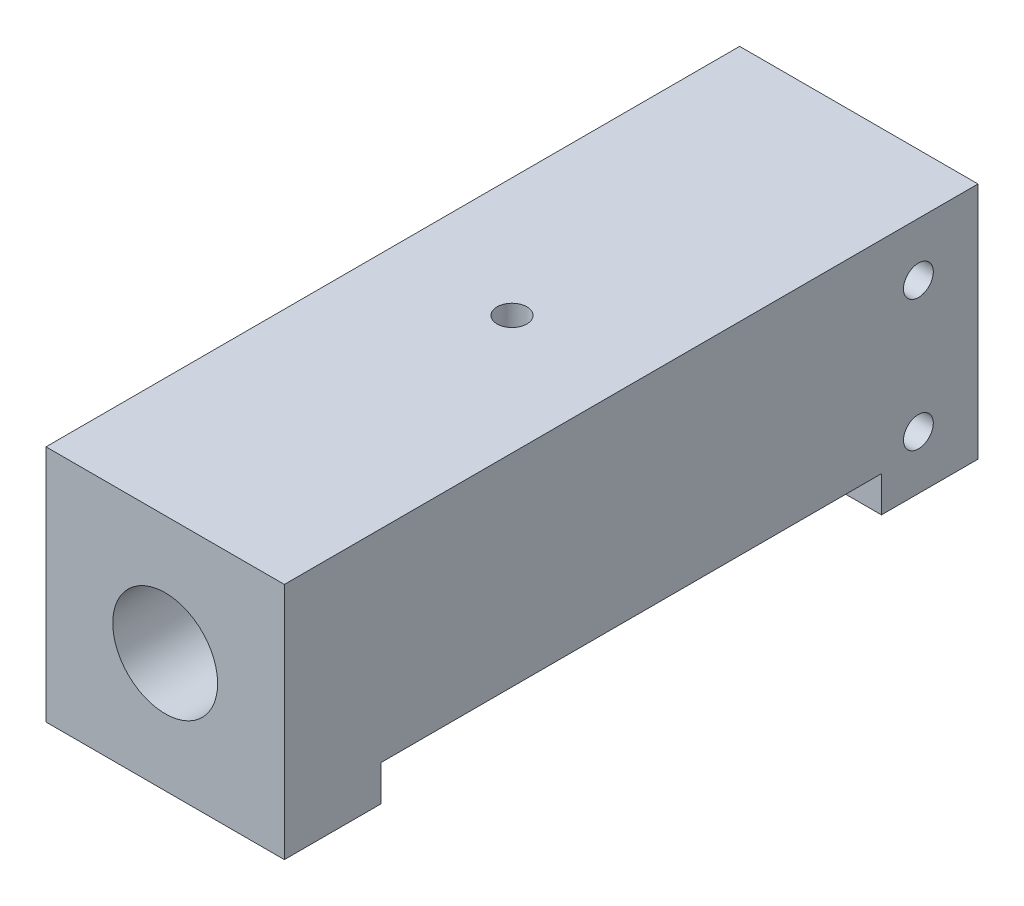
SolidWorks part; units mm, degrees
material "6063-T5"
ref_plane "Piano frontale" through (0, 0, 0) normal (0, 0, 1) x (1, 0, 0)
ref_plane "Piano superiore" through (0, 0, 0) normal (0, 1, 0) x (1, 0, 0)
ref_plane "Piano destro" through (0, 0, 0) normal (1, 0, 0) x (0, 0, -1)
sketch "Schizzo1" plane through (0, 0, 0) normal (0, 0, 1) x (1, 0, 0)
  line L1 (10, -10) -> (-10, -10)
  line L2 (10, -10) -> (10, 10)
  line L3 (10, 10) -> (-10, 10)
  line L4 (-10, -10) -> (-10, 10)
  line L5 (10, -10) -> (-10, 10) construction
  line L6 (10, 10) -> (-10, -10) construction
  point P0 (0, 0)
  dimension "D1" = 20
  dimension "D2" = 20
extrude "Estrusione-Estrusione1" add sketch "Schizzo1" against normal blind 58.2
sketch "Schizzo2" plane through (0, 0, -58.2) normal (0, 0, -1) x (-1, 0, 0)
  circle A0 centre (0, 0) radius 2.05
  dimension "D1" = 4.1
extrude "Taglio-Estrusione1" cut sketch "Schizzo2" against normal through all
sketch "Schizzo3" plane through (0, 0, -58.2) normal (0, 0, -1) x (-1, 0, 0)
  point P0 (0, 0)
hole_wizard "Foro filettato G1/8-1" positions "Schizzo8" profile "Schizzo7" tap size "G1/8" standard "BSI"
sketch "Schizzo8" plane through (0, 0, 0) normal (0, 0, 1) x (1, 0, 0)
  point P0 (0, 0)
sketch "Schizzo7" plane through (0, 0, 0) normal (1, 0, 0) x (0, -1, 0)
  line L0 (0, 0) -> (0, 12.6438)
  line L1 (0, 12.6438) -> (4.4, 10)
  line L2 (4.4, 10) -> (4.4, 0)
  line L5 (4.4, 0) -> (0, 0)
  line L10 (0, 12.6438) -> (-4.4, 10) construction
  line L11 (0, -6.35) -> (0, 107.95) construction
  dimension "Tap Drill Dia." = 8.8
  dimension "Tap Drill Depth" = 10
  dimension "Drill Angle" = 118
sketch "Schizzo11" plane through (0, 10, 0) normal (0, 1, 0) x (1, 0, 0)
  line L0 (0, 58.2) -> (0, 0) construction
  line L1 (10, 58.2) -> (-10, 58.2) construction
  line L2 (10, 29.1) -> (-10, 29.1) construction
  line L3 (10, 58.2) -> (10, 0) construction
  point P10 (0, 29.1)
  point P11 (0, 29.1)
  point P12 (0, 29.1)
hole_wizard "M3 Tapped Hole2" positions "Schizzo3D1" profile "Schizzo12" tap size "M3" standard "DIN"
sketch3d "Schizzo3D1"
  point P0 (0, 10, -29.1)
sketch "Schizzo12" plane through (0, 10, -29.1) normal (1, 0, 0) x (0, 0, 1)
  line L0 (0, 0) -> (0, 5.7511)
  line L1 (0, 5.7511) -> (1.25, 5)
  line L2 (1.25, 5) -> (1.25, 0)
  line L5 (1.25, 0) -> (0, 0)
  line L10 (0, 5.7511) -> (-1.25, 5) construction
  line L11 (0, -6.35) -> (0, 107.95) construction
  dimension "Tap Drill Dia." = 2.5
  dimension "Tap Drill Depth" = 5
  dimension "Drill Angle" = 118
cosmetic thread "Hole Thread4" parameters "D1"=5, "D2"=3
hole_wizard "Foro Ø16.0 (16)-1" positions "Schizzo3D3" profile "Schizzo14" hole size "Ø16.0" standard "ISO"
sketch3d "Schizzo3D3"
  point P0 (0, 0, 0)
  point P3 (0, 0, -58.2)
sketch "Schizzo14" plane through (0, 0, -58.2) normal (1, 0, 0) x (0, 1, 0)
  line L0 (0, 0) -> (0, 16.8069)
  line L1 (0, 16.8069) -> (8, 12)
  line L2 (8, 12) -> (8, 0)
  line L5 (8, 0) -> (0, 0)
  line L10 (0, 16.8069) -> (-8, 12) construction
  line L11 (0, -6.35) -> (0, 107.95) construction
  dimension "Hole Dia." = 16
  dimension "Hole Depth" = 12
  dimension "Drill Angle" = 118
sketch "Schizzo15" plane through (10, 0, 0) normal (1, 0, 0) x (0, 0, -1)
  line L0 (46.2, 0) -> (58.2, 0) construction
  line L1 (46.2, 8) -> (46.2, -8) construction
  line L4 (58.2, -10) -> (58.2, 10) construction
  line L6 (58.2, -10) -> (0, -10) construction
  point P5 (53.2, -5.5)
  point P8 (53.2, 5.5)
  dimension "D1" = 5.5
  dimension "D2" = 7
  dimension "D3" = 5
  dimension "D4" = 4.5
hole_wizard "M3 Tapped Hole3" positions "Schizzo3D4" profile "Schizzo16" tap size "M3" standard "ISO"
sketch3d "Schizzo3D4"
  point P0 (10, 5.5, -53.2)
  point P3 (10, -5.5, -53.2)
sketch "Schizzo16" plane through (10, 5.5, -53.2) normal (0, 1, 0) x (0, 0, -1)
  line L0 (0, 0) -> (0, 4.1905)
  line L1 (0, 4.1905) -> (1.25, 4.1905)
  line L2 (1.25, 4.1905) -> (1.25, 0)
  line L5 (1.25, 0) -> (0, 0)
  line L11 (0, -6.35) -> (0, 107.95) construction
  dimension "Thread Major Dia." = 2.5
  dimension "Thru Tap Drill Depth" = 4.1905
sketch "Sketch1" plane through (-10, 0, 0) normal (-1, 0, 0) x (0, 0, 1)
  line L0 (-58.2, 10) -> (-58.2, -10) construction
  line L1 (-58.2, 3) -> (-22, 3)
  line L2 (-58.2, 3) -> (-58.2, -3)
  line L3 (-58.2, -3) -> (-22, -3)
  line L4 (-22, 3) -> (-22, -3)
  line L5 (0, 10) -> (0, -10) construction
  line L6 (0, 0) -> (-22, 0) construction
  point P8 (-22, 0)
  dimension "D1" = 6
  dimension "D2" = 22
extrude "Boss-Extrude1" add sketch "Sketch1" along normal blind 4.9
sketch "Sketch2" plane through (10, 0, 0) normal (1, 0, 0) x (0, 0, -1)
  line L0 (58.2, -10) -> (0, -10) construction
  line L1 (50.1, -10) -> (34.1, -10)
  line L2 (50.1, -10) -> (50.1, -7)
  line L3 (50.1, -7) -> (34.1, -7)
  line L4 (34.1, -7) -> (8.1, -7)
  line L5 (42.1, -7) -> (42.1, -12.5) construction
  line L6 (8.1, -7) -> (8.1, -10)
  line L7 (8.1, -10) -> (34.1, -10)
  line L8 (0, -10) -> (8.1, -10) construction
  line L9 (50.1, -10) -> (58.2, -10) construction
  dimension "D1" = 16
  dimension "D2" = 3
extrude "Cut-Extrude1" cut sketch "Sketch2" against normal through all
sketch "Sketch3" plane through (0, 0, -22) normal (0, 0, 1) x (1, 0, 0)
  point P0 (-13, 0)
hole_wizard "M3 Tapped Hole4" positions "Sketch6" profile "Sketch7" tap size "M3" standard "ISO"
sketch "Sketch6" plane through (0, 0, -22) normal (0, 0, 1) x (1, 0, 0)
  point P0 (-13, 0)
sketch "Sketch7" plane through (-13, 0, -22) normal (1, 0, 0) x (0, -1, 0)
  line L0 (0, 0) -> (0, 20.7511)
  line L1 (0, 20.7511) -> (1.25, 20)
  line L2 (1.25, 20) -> (1.25, 0)
  line L5 (1.25, 0) -> (0, 0)
  line L10 (0, 20.7511) -> (-1.25, 20) construction
  line L11 (0, -6.35) -> (0, 107.95) construction
  dimension "Tap Drill Dia." = 2.5
  dimension "Tap Drill Depth" = 20
  dimension "Drill Angle" = 118
sketch "Sketch8" plane through (-10, 0, 0) normal (-1, 0, 0) x (0, 0, 1)
  line L1 (0, 10) -> (-58.2, 10) construction
  line L2 (0, 10) -> (0, -10) construction
  line L3 (0, -10) -> (-58.2, -10) construction
  line L4 (-58.2, 10) -> (-58.2, -10) construction
sketch "Sketch9" plane through (0, -10, 0) normal (0, -1, 0) x (1, 0, 0)
  line L1 (14, -8.1) -> (-14, -8.1) construction
  line L2 (14, -8.1) -> (14, -50.1) construction
  line L3 (14, -50.1) -> (-14, -50.1) construction
  line L4 (-14, -8.1) -> (-14, -50.1) construction
  line L6 (-10, -50.1) -> (-3.873, -50.1) construction
  line L7 (-10, -8.1) -> (10, -8.1) construction
  line L8 (10, -50.1) -> (10, -8.1) construction
  line L9 (-10, 0) -> (-10, -58.2) construction
  dimension "D1" = 4
  dimension "D2" = 4
